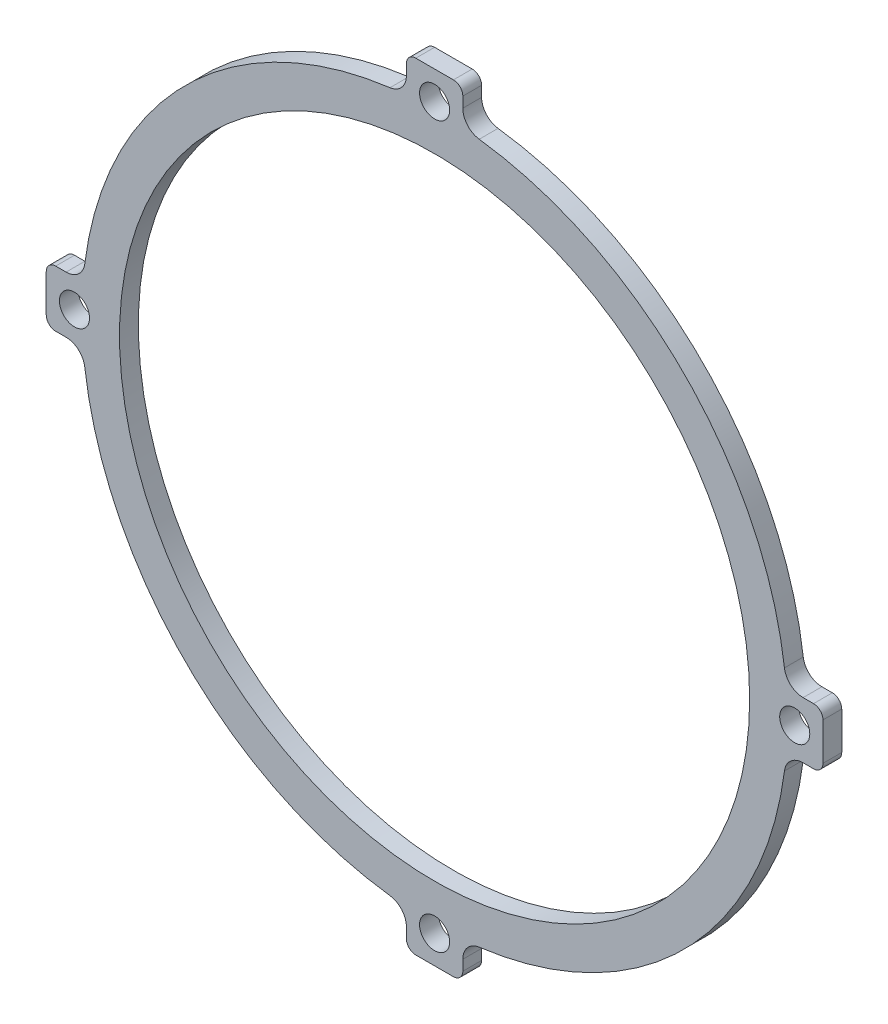
SolidWorks part; units mm, degrees
ref_plane "正面" through (0, 0, 0) normal (0, 0, 1) x (1, 0, 0)
ref_plane "平面" through (0, 0, 0) normal (0, 1, 0) x (1, 0, 0)
ref_plane "右側面" through (0, 0, 0) normal (1, 0, 0) x (0, 0, -1)
sketch "ｽｹｯﾁ1" plane through (0, 0, 0) normal (0, 0, 1) x (1, 0, 0)
  line L12 (-3, -39.1823) -> (-3, -41.2916)
  line L13 (-3, -41.2916) -> (3, -41.2916)
  line L14 (3, -41.2916) -> (3, -39.1823)
  line L15 (39.1823, -3) -> (41.2916, -3)
  line L16 (41.2916, -3) -> (41.2916, 3)
  line L17 (41.2916, 3) -> (39.1823, 3)
  line L18 (3, 39.1823) -> (3, 41.2916)
  line L19 (3, 41.2916) -> (-3, 41.2916)
  line L20 (-3, 41.2916) -> (-3, 39.1823)
  line L21 (-39.1823, 3) -> (-41.2916, 3)
  line L22 (-41.2916, 3) -> (-41.2916, -3)
  line L23 (-41.2916, -3) -> (-39.1823, -3)
  line L24 (-3, -39.1823) -> (-3, -41.2916)
  line L25 (-3, -41.2916) -> (3, -41.2916)
  line L26 (3, -41.2916) -> (3, -39.1823)
  line L27 (39.1823, -3) -> (41.2916, -3)
  line L28 (41.2916, -3) -> (41.2916, 3)
  line L29 (41.2916, 3) -> (39.1823, 3)
  line L30 (3, 39.1823) -> (3, 41.2916)
  line L31 (3, 41.2916) -> (-3, 41.2916)
  line L32 (-3, 41.2916) -> (-3, 39.1823)
  line L33 (-39.1823, 3) -> (-41.2916, 3)
  line L34 (-41.2916, 3) -> (-41.2916, -3)
  line L35 (-41.2916, -3) -> (-39.1823, -3)
  circle A0 centre (-38.2916, 0) radius 1.6 construction
  circle A1 centre (0, -38.2916) radius 1.6 construction
  circle A2 centre (0, 38.2916) radius 1.6 construction
  circle A3 centre (38.2916, 0) radius 1.6 construction
  circle A4 centre (-38.2916, 0) radius 1.6
  circle A5 centre (0, -38.2916) radius 1.6
  circle A6 centre (0, 38.2916) radius 1.6
  circle A7 centre (38.2916, 0) radius 1.6
  arc A12 (-3, -39.1823) -> (-4.7468, -37.1984) centre (-5, -39.1823) ccw
  arc A13 (4.7468, -37.1984) -> (3, -39.1823) centre (5, -39.1823) ccw
  arc A14 (4.7468, -37.1984) -> (37.1984, -4.7468) centre (0, 0) ccw
  arc A15 (39.1823, -3) -> (37.1984, -4.7468) centre (39.1823, -5) ccw
  arc A16 (37.1984, 4.7468) -> (39.1823, 3) centre (39.1823, 5) ccw
  arc A17 (37.1984, 4.7468) -> (4.7468, 37.1984) centre (0, 0) ccw
  arc A18 (3, 39.1823) -> (4.7468, 37.1984) centre (5, 39.1823) ccw
  arc A19 (-4.7468, 37.1984) -> (-3, 39.1823) centre (-5, 39.1823) ccw
  arc A20 (-4.7468, 37.1984) -> (-37.1984, 4.7468) centre (0, 0) ccw
  arc A21 (-39.1823, 3) -> (-37.1984, 4.7468) centre (-39.1823, 5) ccw
  arc A22 (-37.1984, -4.7468) -> (-39.1823, -3) centre (-39.1823, -5) ccw
  arc A23 (-37.1984, -4.7468) -> (-4.7468, -37.1984) centre (0, 0) ccw
  arc A24 (-3, -39.1823) -> (-4.7468, -37.1984) centre (-5, -39.1823) ccw
  arc A25 (4.7468, -37.1984) -> (3, -39.1823) centre (5, -39.1823) ccw
  arc A26 (4.7468, -37.1984) -> (37.1984, -4.7468) centre (0, 0) ccw
  arc A27 (39.1823, -3) -> (37.1984, -4.7468) centre (39.1823, -5) ccw
  arc A28 (37.1984, 4.7468) -> (39.1823, 3) centre (39.1823, 5) ccw
  arc A29 (37.1984, 4.7468) -> (4.7468, 37.1984) centre (0, 0) ccw
  arc A30 (3, 39.1823) -> (4.7468, 37.1984) centre (5, 39.1823) ccw
  arc A31 (-4.7468, 37.1984) -> (-3, 39.1823) centre (-5, 39.1823) ccw
  arc A32 (-4.7468, 37.1984) -> (-37.1984, 4.7468) centre (0, 0) ccw
  arc A33 (-39.1823, 3) -> (-37.1984, 4.7468) centre (-39.1823, 5) ccw
  arc A34 (-37.1984, -4.7468) -> (-39.1823, -3) centre (-39.1823, -5) ccw
  arc A35 (-37.1984, -4.7468) -> (-4.7468, -37.1984) centre (0, 0) ccw
  dimension "D1" = 0
extrude "ﾎﾞｽ - 押し出し1" add sketch "ｽｹｯﾁ1" along normal blind 2
sketch "ｽｹｯﾁ3" plane through (0, 0, 2) normal (0, 0, 1) x (1, 0, 0)
  circle A0 centre (0, 0) radius 4.5
  circle A1 centre (0, 8.5) radius 1.25
  circle A2 centre (8.5, 0) radius 1.25
  circle A3 centre (0, -8.5) radius 1.25
  circle A4 centre (-8.5, 0) radius 1.25
  point P14 (0, 0)
  dimension "D1" = 9
  dimension "D2" = 2.5
  dimension "D3" = 8.5
  dimension "D4" = 4
extrude "ｶｯﾄ - 押し出し1" cut sketch "ｽｹｯﾁ3" against normal through all
sketch "ｽｹｯﾁ4" plane through (0, 0, 2) normal (0, 0, 1) x (1, 0, 0)
  line L0 (0, 33.5) -> (0, 0) construction
  line L1 (-3, 33.3654) -> (-3, 12.1347)
  line L2 (3, 33.3654) -> (3, 12.1347)
  line L3 (33.3654, 3) -> (12.1347, 3)
  line L4 (33.3654, -3) -> (12.1347, -3)
  line L5 (3, -33.3654) -> (3, -12.1347)
  line L6 (-3, -33.3654) -> (-3, -12.1347)
  line L7 (-33.3654, -3) -> (-12.1347, -3)
  line L8 (-33.3654, 3) -> (-12.1347, 3)
  arc A0 (-3, 12.1347) -> (-12.1347, 3) centre (0, 0) ccw
  arc A1 (-3, 33.3654) -> (-33.3654, 3) centre (0, 0) ccw
  arc A2 (37.1984, 4.7468) -> (4.7468, 37.1984) centre (0, 0) ccw construction
  arc A3 (33.3654, 3) -> (3, 33.3654) centre (0, 0) ccw
  arc A4 (12.1347, 3) -> (3, 12.1347) centre (0, 0) ccw
  arc A5 (3, -12.1347) -> (12.1347, -3) centre (0, 0) ccw
  arc A6 (3, -33.3654) -> (33.3654, -3) centre (0, 0) ccw
  arc A7 (-12.1347, -3) -> (-3, -12.1347) centre (0, 0) ccw
  arc A8 (-33.3654, -3) -> (-3, -33.3654) centre (0, 0) ccw
  point P27 (0, 0)
  dimension "D3" = 4
  dimension "D4" = 25
  dimension "D1" = 3
  dimension "D2" = 3
  dimension "D5" = 4
extrude "ｶｯﾄ - 押し出し2" cut sketch "ｽｹｯﾁ4" against normal through all
fillet "ﾌｨﾚｯﾄ1" radius 1 8 edges at (41.2916, 3, 1) (41.2916, -3, 1) (3, -41.2916, 1) (-3, -41.2916, 1) (-41.2916, -3, 1) (-41.2916, 3, 1) (-3, 41.2916, 1) (3, 41.2916, 1)
sketch "ｽｹｯﾁ5" plane through (0, 0, 2) normal (0, 0, 1) x (1, 0, 0)
  circle A0 centre (0, 0) radius 33.5
extrude "ｶｯﾄ - 押し出し3" cut sketch "ｽｹｯﾁ5" against normal through all
